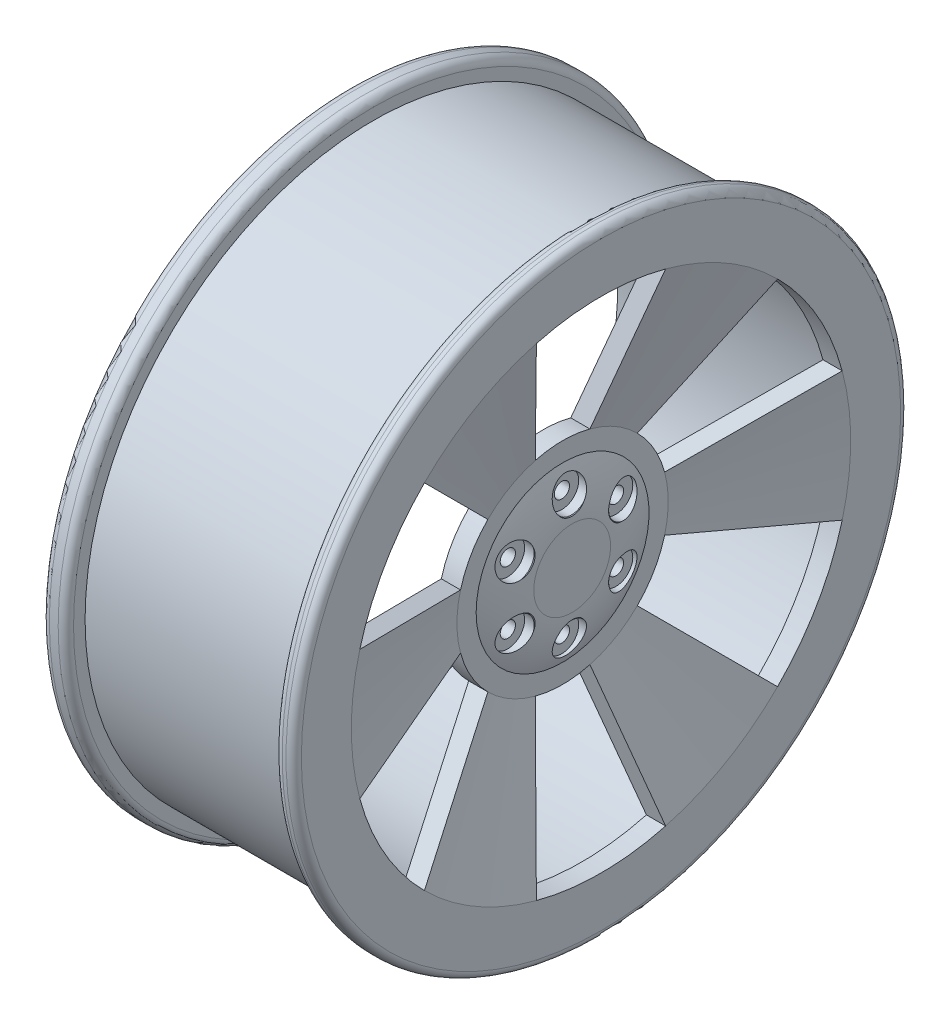
SolidWorks part; units mm, degrees
ref_plane "Front Plane" through (0, 0, 0) normal (0, 0, 1) x (1, 0, 0)
ref_plane "Top Plane" through (0, 0, 0) normal (0, 1, 0) x (1, 0, 0)
ref_plane "Right Plane" through (0, 0, 0) normal (1, 0, 0) x (0, 0, -1)
sketch "Sketch1" plane through (0, 0, 0) normal (1, 0, 0) x (0, 0, -1)
  circle A0 centre (0, 0) radius 190.5
  dimension "D1" = 381
extrude "Boss-Extrude1" add sketch "Sketch1" along normal blind 166.624 contours A0
sketch "Sketch4" plane through (166.624, 0, 0) normal (1, 0, 0) x (0, 0, -1)
  circle A0 centre (0, 0) radius 203.2
  dimension "D1" = 406.4
extrude "Boss-Extrude2" add sketch "Sketch4" against normal blind 12.7
sketch "Sketch5" plane through (0, 0, 0) normal (-1, 0, 0) x (0, 0, 1)
  circle A0 centre (0, 0) radius 203.2
  dimension "D1" = 406.4
extrude "Boss-Extrude3" add sketch "Sketch5" against normal blind 16.002
sketch "Sketch6" plane through (0, 0, 0) normal (-1, 0, 0) x (0, 0, 1)
  circle A0 centre (0, 0) radius 177.8
  dimension "D1" = 355.6
extrude "Cut-Extrude2" cut sketch "Sketch6" against normal blind 153.924
sketch "Sketch7" plane through (166.624, 0, 0) normal (1, 0, 0) x (0, 0, -1)
  circle A0 centre (0, 0) radius 165.1
  dimension "D1" = 330.2
extrude "Cut-Extrude3" cut sketch "Sketch7" against normal blind 12.7
fillet "Fillet1" radius 5.08 4 edges at (16.002, 0, 203.2) (0, 0, 203.2) (153.924, 0, -203.2) (166.624, 0, -203.2)
sketch "Sketch9" plane through (0, 0, 0) normal (0, 0, 1) x (1, 0, 0)
  line L0 (141.224, 69.85) -> (141.224, 0)
  line L1 (166.624, -198.12) -> (166.624, 198.12) construction
  line L2 (141.224, 69.85) -> (166.624, 165.1)
  line L3 (166.624, -165.1) -> (166.624, 165.1) construction
  line L4 (166.624, 165.1) -> (153.924, 165.1)
  line L5 (153.924, 177.8) -> (153.924, -177.8) construction
  line L6 (153.924, 198.12) -> (153.924, -198.12) construction
  line L7 (141.224, 0) -> (128.524, 0)
  line L8 (128.524, 0) -> (128.524, 69.85)
  line L9 (128.524, 69.85) -> (153.924, 165.1)
  dimension "D1" = 0
  dimension "D2" = 69.85
  dimension "D3" = 25.4
  dimension "D4" = 12.7
revolve "Revolve1" add sketch "Sketch9" angle 360 about L7
sketch "Sketch10" plane through (128.524, 0, 0) normal (-1, 0, 0) x (0, 0, 1)
  line L1 (18.0785, 67.4699) -> (42.731, 159.4744)
  line L2 (-18.0785, 67.4699) -> (-42.731, 159.4744)
  arc A0 (42.731, 159.4744) -> (-42.731, 159.4744) centre (0, 0) ccw
  arc A1 (18.0785, 67.4699) -> (-18.0785, 67.4699) centre (0, 0) ccw
  dimension "D1" = 330.2
  dimension "D2" = 139.7
extrude "Cut-Extrude4" cut sketch "Sketch10" against normal blind 50.8
ref_axis "Axis1" through (-8.3312, 0, 0) along (1, 0, 0)
pattern_circular "CirPattern1" count 6 over 360 about axis through (0, 0, 0) along (1, 0, 0) of "Cut-Extrude4"
sketch "Sketch12" plane through (141.224, 0, 0) normal (1, 0, 0) x (0, 0, -1)
  circle A0 centre (0, 0) radius 25.4
  dimension "D1" = 50.8
extrude "Boss-Extrude4" add sketch "Sketch12" along normal blind 6.35
sketch "Sketch13" plane through (0, 0, 0) normal (0, 0, 1) x (1, 0, 0)
  line L0 (147.574, 25.4) -> (141.224, 25.4)
  line L1 (147.574, -25.4) -> (147.574, 25.4) construction
  line L2 (141.224, -25.4) -> (141.224, 25.4) construction
  line L3 (141.224, 18.0785) -> (141.224, 49.3914) construction
  line L4 (141.224, 25.4) -> (141.224, 57.15)
  arc A0 (147.574, 25.4) -> (141.224, 57.15) centre (65.024, 25.4) ccw
  dimension "D1" = 31.75
revolve "Revolve2" add sketch "Sketch13" angle 360 about axis through (-8.3312, 0, 0) along (1, 0, 0)
hole_wizard "CBORE for 3/8 Hex Cap Screw2" positions "Sketch18" profile "Sketch19" counterbore size "3/8" standard "ANSI Inch" end condition through all
sketch "Sketch18" plane through (147.574, 0, 0) normal (1, 0, 0) x (0, 0, -1)
  point P0 (0, 41.275)
  dimension "D1" = 41.275
sketch "Sketch19" plane through (147.574, 41.275, 0) normal (0, 1, 0) x (0, 0, -1)
  line L0 (0, 0) -> (0, 147.574)
  line L1 (0, 147.574) -> (5.0419, 147.574)
  line L3 (5.0419, 147.574) -> (5.0419, 6.8072)
  line L4 (11.1125, 6.8072) -> (5.0419, 6.8072)
  line L5 (11.1125, 6.8072) -> (11.1125, 0.5328)
  line L6 (11.1125, 0.5328) -> (11.7475, 0)
  line L7 (11.7475, 0) -> (0, 0)
  line L8 (-11.1125, 0.5328) -> (-11.7475, 0) construction
  line L11 (0, -6.35) -> (0, 107.95) construction
  dimension "Thru Hole Dia." = 10.0838
  dimension "Thru Hole Depth" = 147.574
  dimension "C'Bore Dia." = 22.225
  dimension "C'Bore Depth" = 6.8072
  dimension "Near C'Sink Dia." = 23.495
  dimension "Near C'Sink Angle" = 100
pattern_circular "CirPattern3" count 6 over 360 about axis through (0, 0, 0) along (1, 0, 0) of "CBORE for 3/8 Hex Cap Screw2"
